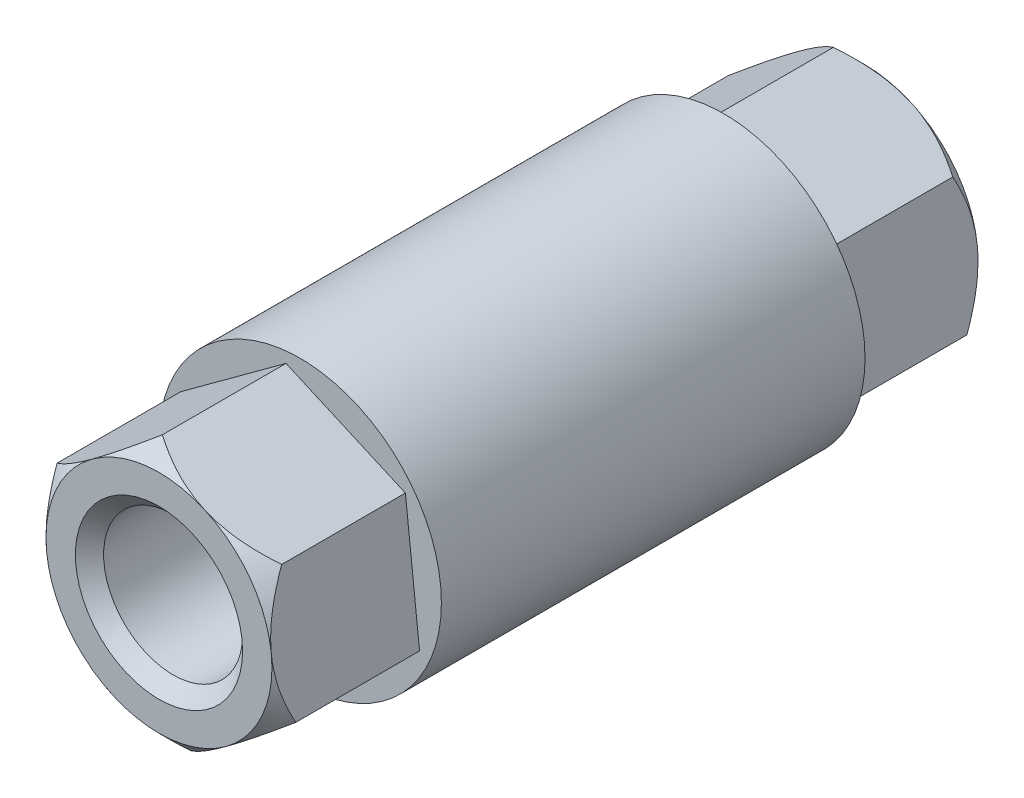
SolidWorks part; units mm, degrees
material "7075-T6 (SN)"
ref_plane "Płaszczyzna XY" through (0, 0, 0) normal (0, 0, 1) x (1, 0, 0)
ref_plane "Płaszczyzna XZ" through (0, 0, 0) normal (0, 1, 0) x (1, 0, 0)
ref_plane "Płaszczyzna YZ" through (0, 0, 0) normal (1, 0, 0) x (0, 0, -1)
sketch "Sketch1" plane through (0, 0, 0) normal (0, 0, 1) x (1, 0, 0)
  circle A0 centre (0, 0) radius 5
  dimension "D1" = 10
extrude "Boss-Extrude1" add sketch "Sketch1" along normal mid plane 15
sketch "Sketch2" plane through (0, 0, 7.5) normal (0, 0, 1) x (1, 0, 0)
  line L1 (0.5016, -4.5915) -> (4.2271, -1.8613)
  line L2 (4.2271, -1.8613) -> (3.7255, 2.7301)
  line L3 (3.7255, 2.7301) -> (-0.5016, 4.5915)
  line L4 (-0.5016, 4.5915) -> (-4.2271, 1.8613)
  line L5 (-4.2271, 1.8613) -> (-3.7255, -2.7301)
  line L6 (-3.7255, -2.7301) -> (0.5016, -4.5915)
  circle A0 centre (0, 0) radius 4 construction
  dimension "D1" = 8
extrude "Boss-Extrude2" add sketch "Sketch2" along normal blind 5
mirror "Mirror1" about plane through (0, 0, 0) normal (0, 0, 1) of "Boss-Extrude2"
sketch "Sketch3" plane through (0, 0, 12.5) normal (0, 0, 1) x (1, 0, 0)
  circle A0 centre (0, 0) radius 2.46
  dimension "D1" = 4.92
extrude "Cut-Extrude1" cut sketch "Sketch3" against normal through all both and the other way through all
chamfer "Chamfer1" distance 0.5 angle 45 2 edges at (2.46, 0, -12.5) (2.46, 0, 12.5)
ref_axis "Axis1" through (0, 0, -12) along (0, 0, 1)
ref_plane "Plane2" through (0, 0, 0) normal (-0.403, -0.9152, 0) x (-0.9152, 0.403, 0)
sketch "Sketch8" plane through (0, 0, 0) normal (-0.403, -0.9152, 0) x (-0.9152, 0.403, 0)
  line L3 (4, 12.5) -> (4.6188, 12.5)
  line L4 (4.6188, 12.5) -> (4.6188, 11.8812)
  line L5 (4.6188, 12.5) -> (4.6188, 7.5) construction
  line L6 (4.6188, 11.8812) -> (4, 12.5)
  point P3 (0, 30)
  dimension "D1" = 0.6188
  dimension "D2" = 0.6188
  dimension "D3" = 45
revolve "Cut-Revolve3" cut sketch "Sketch8" angle 360 about axis through (0, 0, -12) along (0, 0, 1)
mirror "Mirror2" about plane through (0, 0, 0) normal (0, 0, 1) of "Cut-Revolve3"
sketch3d "3DSketch1"
  line L0 (0, 0, -28.69) -> (0, 0, 28.69)
  point P5 (0, 0, 0)
  dimension "D1" = 57.38
